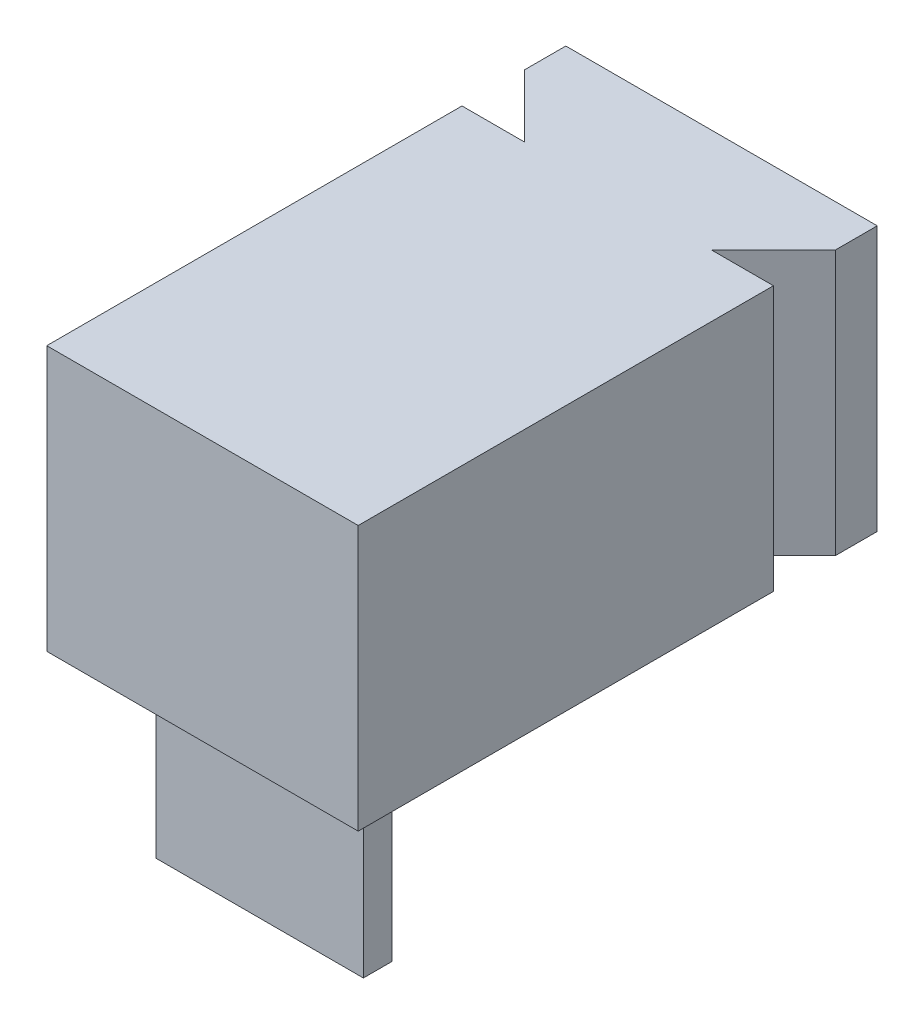
SolidWorks part; units mm, degrees
ref_plane "Front Plane" through (0, 0, 0) normal (0, 0, 1) x (1, 0, 0)
ref_plane "Top Plane" through (0, 0, 0) normal (0, 1, 0) x (1, 0, 0)
ref_plane "Right Plane" through (0, 0, 0) normal (1, 0, 0) x (0, 0, -1)
sketch "Sketch1" plane through (0, 0, 0) normal (0, 1, 0) x (1, 0, 0)
  line L1 (-3, -4) -> (3, -4)
  line L2 (-3, -4) -> (-3, 4)
  line L3 (-3, 4) -> (3, 4)
  line L4 (3, -4) -> (3, 4)
  line L5 (-3, -4) -> (3, 4) construction
  line L6 (-3, 4) -> (3, -4) construction
  point P0 (0, 0)
  dimension "D1" = 6
  dimension "D2" = 8
extrude "Boss-Extrude1" add sketch "Sketch1" along normal blind 5.1
sketch "Sketch2" plane through (0, 0, 0) normal (0, -1, 0) x (1, 0, 0)
  line L0 (3, -6) -> (-3, -6)
  line L1 (-3, -6) -> (-3, -5.2)
  line L2 (-3, -5.2) -> (-1.8, -4)
  line L3 (3, -4) -> (-3, -4) construction
  line L4 (-1.8, -4) -> (1.8, -4)
  line L5 (1.8, -4) -> (3, -5.2)
  line L6 (3, -5.2) -> (3, -6)
  line L7 (-3, 4) -> (3, 4) construction
  line L8 (3, 4) -> (3, -4) construction
  point P2 (0, -6)
  dimension "D1" = 10
  dimension "D2" = 45
  dimension "D3" = 0.8
extrude "Boss-Extrude2" add sketch "Sketch2" against normal up to surface (5.1 mm away) up to face at (0, 5.1, 0)
sketch "Sketch3" plane through (0, 0, 0) normal (0, -1, 0) x (1, 0, 0)
  line L0 (-3, 4) -> (3, 4) construction
  line L1 (-2, 2.35) -> (2, 2.35)
  line L2 (-2, 2.35) -> (-2, 2.9)
  line L3 (-2, 2.9) -> (2, 2.9)
  line L4 (2, 2.35) -> (2, 2.9)
  line L5 (-2, 2.35) -> (2, 2.9) construction
  line L6 (-2, 2.9) -> (2, 2.35) construction
  line L7 (-3, -4) -> (-3, 4) construction
  line L8 (3, 4) -> (3, -4) construction
  point P0 (0, 2.625)
  dimension "D1" = 1.1
  dimension "D2" = 0.55
  dimension "D3" = 1
  dimension "D4" = 1
extrude "Boss-Extrude3" add sketch "Sketch3" along normal blind 3.5
